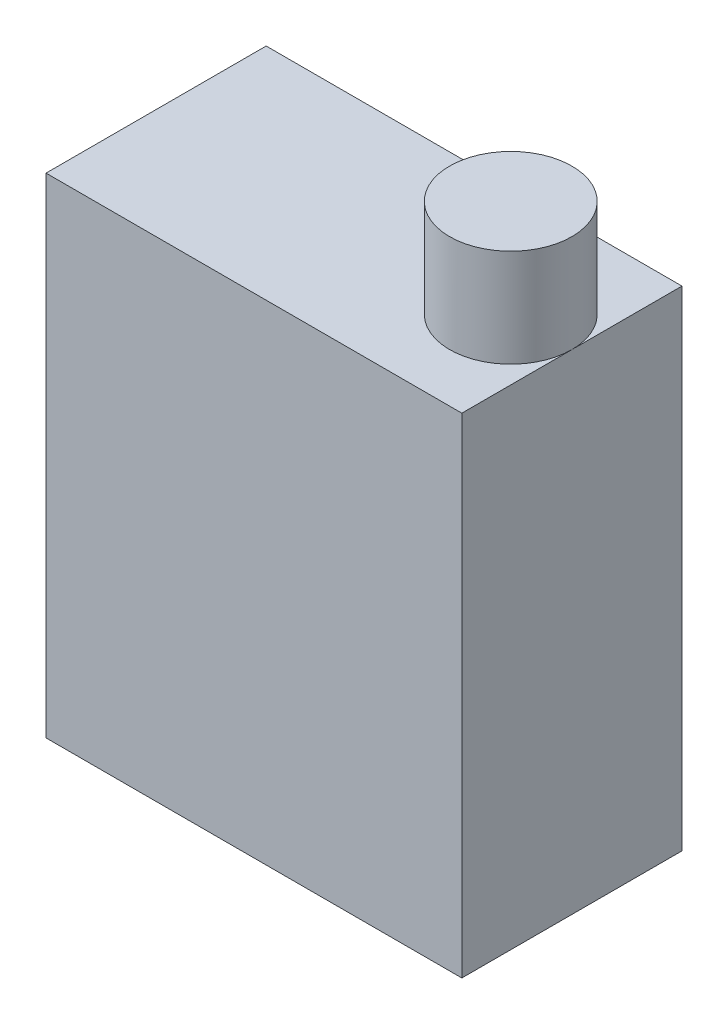
SolidWorks part; units mm, degrees
ref_plane "Front Plane" through (0, 0, 0) normal (0, 0, 1) x (1, 0, 0)
ref_plane "Top Plane" through (0, 0, 0) normal (0, 1, 0) x (1, 0, 0)
ref_plane "Right Plane" through (0, 0, 0) normal (1, 0, 0) x (0, 0, -1)
sketch "Sketch1" plane through (0, 0, 0) normal (0, 1, 0) x (1, 0, 0)
  line L1 (-4.9784, 0.8636) -> (-0.6604, 0.8636)
  line L2 (-4.9784, 0.8636) -> (-4.9784, -1.4224)
  line L3 (-4.9784, -1.4224) -> (-0.6604, -1.4224)
  line L4 (-0.6604, 0.8636) -> (-0.6604, -1.4224)
  dimension "D1" = 4.318
  dimension "D2" = 2.286
extrude "Boss-Extrude1" add sketch "Sketch1" along normal blind 5.08
sketch "Sketch2" plane through (0, 5.08, 0) normal (0, 1, 0) x (1, 0, 0)
  line L0 (-4.9784, -1.4224) -> (-0.6604, -1.4224) construction
  line L2 (-0.6604, -1.4224) -> (-0.6604, 0.8636) construction
  circle A0 centre (-1.2954, -0.2794) radius 0.635
  point P4 (-2.4916, -0.2794)
  dimension "D1" = 1.27
  dimension "D3" = 0.635
  dimension "D2" = 1.143
extrude "Boss-Extrude2" add sketch "Sketch2" along normal blind 1.016
